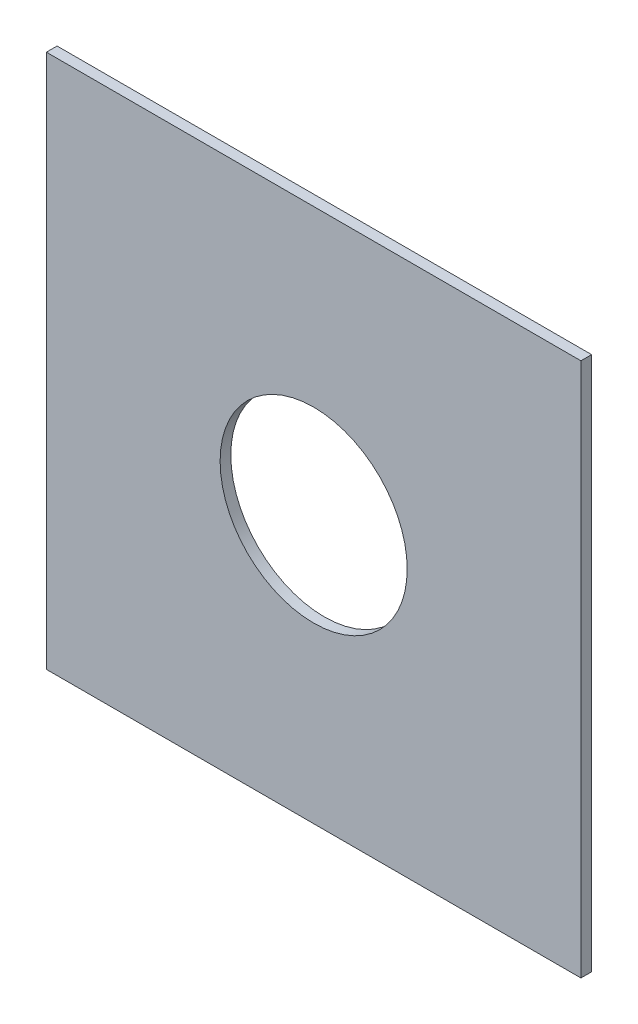
SolidWorks part; units mm, degrees
ref_plane "Front Plane" through (0, 0, 0) normal (0, 0, 1) x (1, 0, 0)
ref_plane "Top Plane" through (0, 0, 0) normal (0, 1, 0) x (1, 0, 0)
ref_plane "Right Plane" through (0, 0, 0) normal (1, 0, 0) x (0, 0, -1)
sketch "Sketch1" plane through (0, 0, 0) normal (0, 0, 1) x (1, 0, 0)
  line L0 (-309.3015, -148.5737) -> (-209.3015, -148.5737) construction
  line L1 (-309.3015, -98.5737) -> (-209.3015, -98.5737)
  line L2 (-309.3015, -98.5737) -> (-309.3015, -198.5737)
  line L3 (-309.3015, -198.5737) -> (-209.3015, -198.5737)
  line L4 (-209.3015, -98.5737) -> (-209.3015, -198.5737)
  line L5 (-259.3015, -98.5737) -> (-259.3015, -198.5737) construction
  circle A0 centre (-259.3015, -148.5737) radius 17.5
  circle A1 centre (-259.3015, -148.5737) radius 17 construction
  circle A2 centre (-259.3015, -148.5737) radius 15 construction
  dimension "D3" = 0
  dimension "D5" = 35
  dimension "D1" = 100
  dimension "D2" = 100
  dimension "D4" = 0
extrude "Boss-Extrude1" add sketch "Sketch1" along normal blind 2 contours L1 L4 L3 L2
sketch "Sketch2" plane through (0, 0, 0) normal (0, 0, -1) x (-1, 0, 0)
  circle A1 centre (258.9447, -122.5737) radius 2.5
  circle A2 centre (285.3015, -155.2168) radius 2.5
  circle A3 centre (259.6584, -181.5737) radius 2.5
  circle A4 centre (226.3015, -148.9306) radius 2.5
  circle A5 centre (259.3015, -148.5737) radius 33.0019 construction
  dimension "D1" = 5
  dimension "D2" = 5
  dimension "D3" = 5
  dimension "D4" = 5
extrude "Cut-Extrude1" [suppressed] cut sketch "Sketch2" against normal through all
